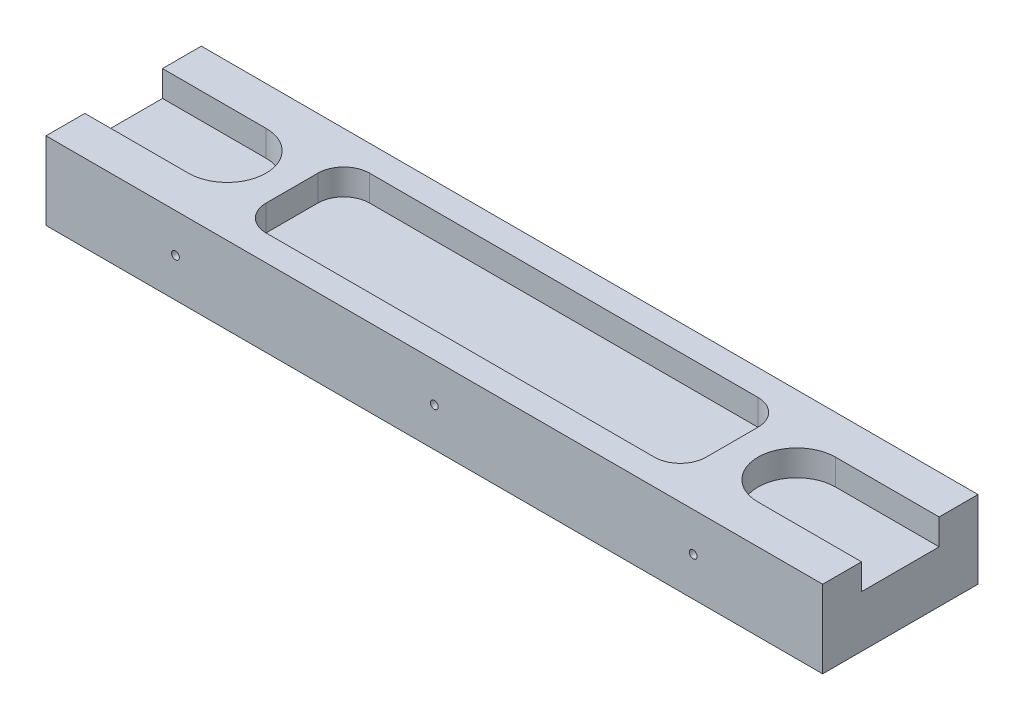
SolidWorks part; units mm, degrees
ref_plane "Front Plane" through (0, 0, 0) normal (0, 0, 1) x (1, 0, 0)
ref_plane "Top Plane" through (0, 0, 0) normal (0, 1, 0) x (1, 0, 0)
ref_plane "Right Plane" through (0, 0, 0) normal (1, 0, 0) x (0, 0, -1)
sketch "Sketch1" plane through (0, 0, 0) normal (0, 1, 0) x (1, 0, 0)
  line L1 (0, 0) -> (150, 0)
  line L2 (0, 0) -> (0, 30)
  line L3 (0, 30) -> (150, 30)
  line L4 (150, 0) -> (150, 30)
  dimension "D1" = 150
  dimension "D2" = 30
extrude "Boss-Extrude1" add sketch "Sketch1" along normal blind 15
sketch "Sketch2" plane through (0, 15, 0) normal (0, 1, 0) x (1, 0, 0)
  line L0 (-20, 15) -> (20, 15) construction
  line L1 (-20, 22.5) -> (20, 22.5)
  line L2 (-20, 7.5) -> (20, 7.5)
  line L3 (0, 30) -> (0, 0) construction
  line L4 (75, 30) -> (75, 0) construction
  line L5 (150, 30) -> (0, 30) construction
  line L6 (0, 0) -> (150, 0) construction
  line L7 (170, 15) -> (130, 15) construction
  line L8 (170, 22.5) -> (130, 22.5)
  line L9 (170, 7.5) -> (130, 7.5)
  arc A0 (-20, 22.5) -> (-20, 7.5) centre (-20, 15) ccw
  arc A1 (20, 7.5) -> (20, 22.5) centre (20, 15) ccw
  arc A2 (170, 22.5) -> (170, 7.5) centre (170, 15) cw
  arc A3 (130, 7.5) -> (130, 22.5) centre (130, 15) cw
  point P2 (0, 15)
  point P9 (0, 15)
  point P18 (150, 15)
  dimension "D1" = 40
  dimension "D2" = 15
extrude "Cut-Extrude1" cut sketch "Sketch2" against normal blind 5
sketch "Sketch3" plane through (0, 0, 0) normal (0, 0, 1) x (1, 0, 0)
  line L0 (0, 7.5) -> (150, 7.5) construction
  line L1 (0, 15) -> (0, 0) construction
  line L2 (150, 15) -> (150, 0) construction
  circle A0 centre (25, 7.5) radius 0.75
  circle A1 centre (75, 7.5) radius 0.75
  circle A2 centre (125, 7.5) radius 0.75
  dimension "D2" = 1.5
  dimension "D1" = 25
  dimension "D3" = 3
extrude "Cut-Extrude2" cut sketch "Sketch3" against normal up to surface (30 mm away) up to face at (75, 7.5, -30)
sketch "Sketch4" plane through (0, 15, 0) normal (0, 1, 0) x (1, 0, 0)
  line L0 (150, 30) -> (0, 30) construction
  line L1 (37.5, 25) -> (112.5, 25)
  line L2 (32.5, 20) -> (32.5, 10)
  line L3 (37.5, 5) -> (112.5, 5)
  line L4 (117.5, 20) -> (117.5, 10)
  line L5 (0, 0) -> (150, 0) construction
  arc A0 (20, 7.5) -> (20, 22.5) centre (20, 15) ccw construction
  arc A1 (130, 22.5) -> (130, 7.5) centre (130, 15) ccw construction
  arc A2 (112.5, 25) -> (117.5, 20) centre (112.5, 20) cw
  arc A3 (112.5, 5) -> (117.5, 10) centre (112.5, 10) ccw
  arc A4 (32.5, 10) -> (37.5, 5) centre (37.5, 10) ccw
  arc A5 (37.5, 25) -> (32.5, 20) centre (37.5, 20) ccw
  point P4 (27.5, 15)
  point P5 (122.5, 15)
  dimension "D5" = 5
  dimension "D1" = 5
  dimension "D2" = 5
  dimension "D3" = 5
  dimension "D4" = 5
extrude "Cut-Extrude3" cut sketch "Sketch4" against normal blind 5
